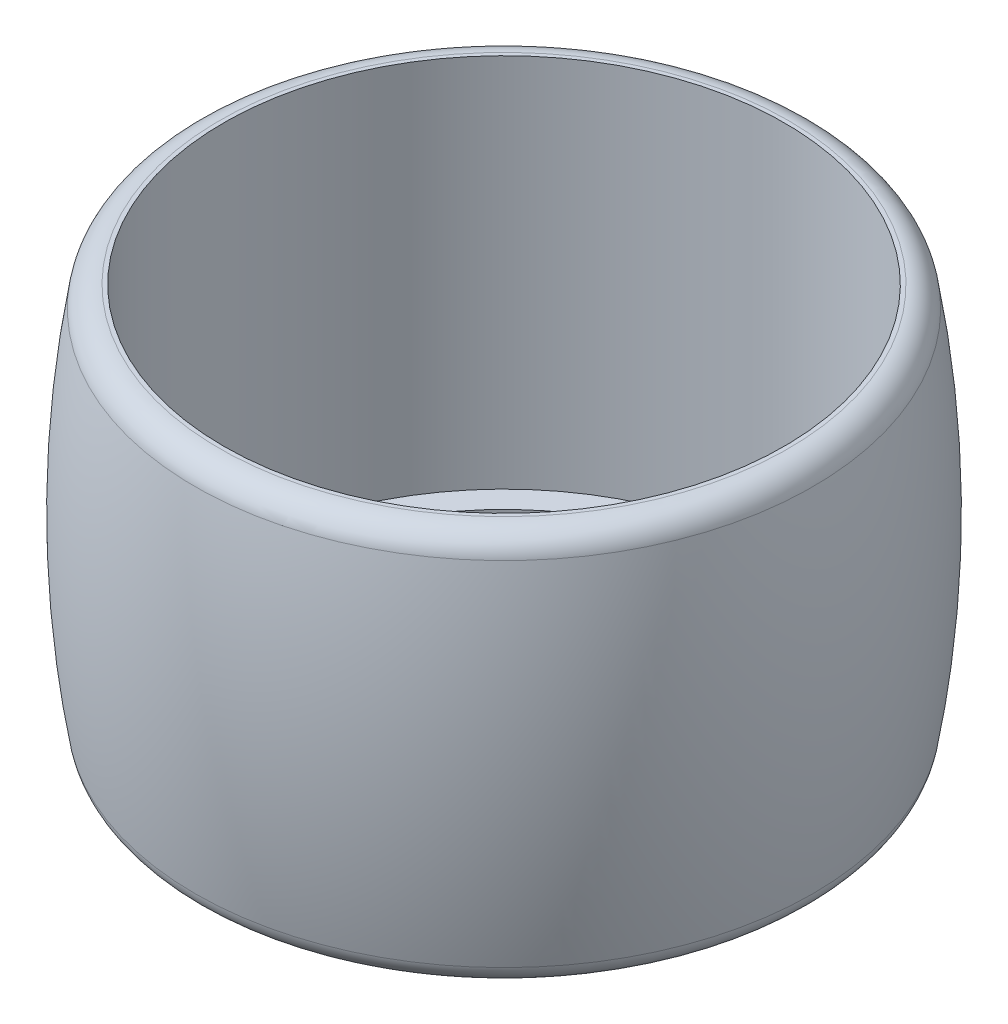
SolidWorks part; units mm, degrees
material "POLYURETHANE (11671)"
ref_plane "Front Plane" through (0, 0, 0) normal (0, 0, 1) x (1, 0, 0)
ref_plane "Top Plane" through (0, 0, 0) normal (0, 1, 0) x (1, 0, 0)
ref_plane "Right Plane" through (0, 0, 0) normal (1, 0, 0) x (0, 0, -1)
sketch "Sketch1" plane through (0, 0, 0) normal (0, 0, 1) x (1, 0, 0)
  line L8 (0, 7.386) -> (0, -6.378) construction
  line L9 (-7.6015, 0) -> (9.1971, 0) construction
  line L10 (20.55, -14.35) -> (22.55, -14.35)
  line L11 (22.55, -14.35) -> (22.55, 15.85)
  line L14 (22.55, 15.85) -> (24.55, 15.85)
  line L16 (24.55, -15.85) -> (20.55, -15.85)
  line L17 (20.55, -15.85) -> (20.55, -14.35)
  arc A0 (24.55, 15.85) -> (24.55, -15.85) centre (-60, 0) cw
other "Pen Sketch1" parameters "D1"=70.898, "D2"=12.5015, "D3"=28.2028, "D4"=34.9, "D5"=3, "D6"=22.6476
revolve "Revolve3" add sketch "Sketch1" angle 360 about L8
fillet "Fillet1" radius 2 2 edges at (0, -15.85, 24.55) (0, 15.85, 24.55)
